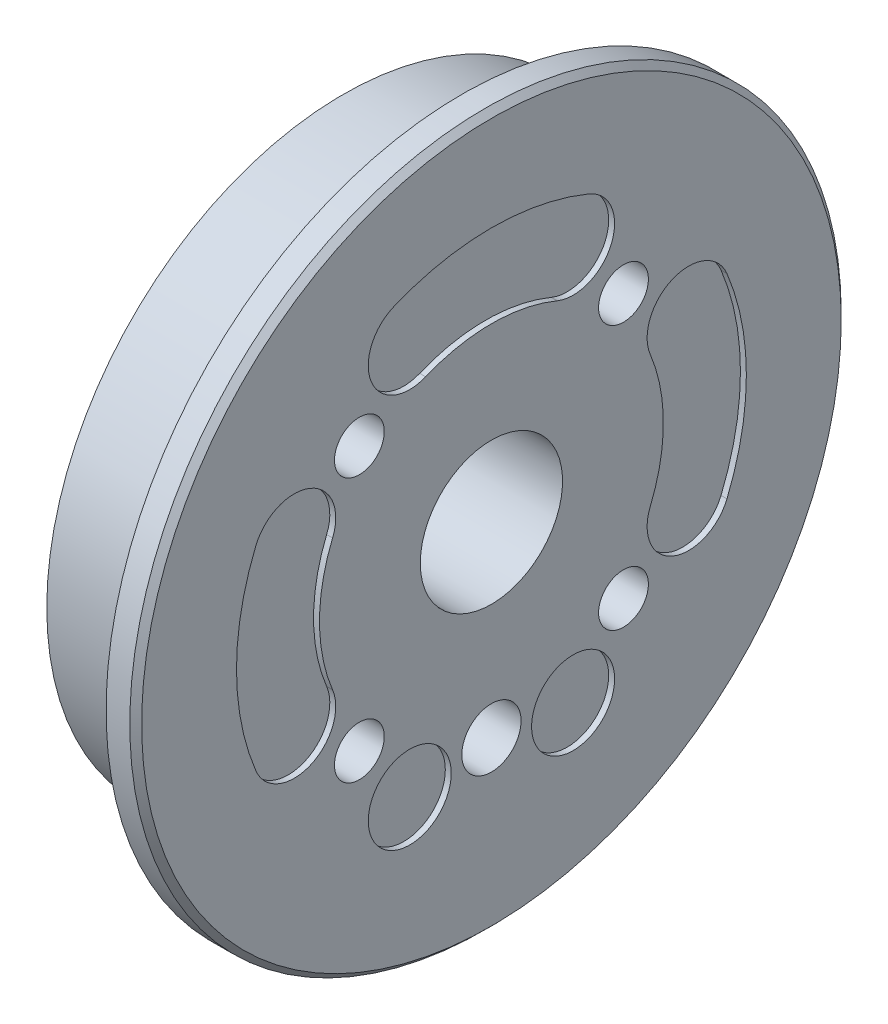
SolidWorks part; units mm, degrees
ref_plane "Front Plane" through (0, 0, 0) normal (0, 0, 1) x (1, 0, 0)
ref_plane "Top Plane" through (0, 0, 0) normal (0, 1, 0) x (1, 0, 0)
ref_plane "Right Plane" through (0, 0, 0) normal (1, 0, 0) x (0, 0, -1)
sketch "Sketch1" plane through (0, 0, 0) normal (0, 0, 1) x (1, 0, 0)
  line L0 (10, 30) -> (10, 0)
  line L1 (10, 0) -> (12.5, 0)
  line L2 (12.5, 0) -> (12.5, 30)
  line L3 (12.5, 30) -> (10, 30)
  line L4 (10, 0) -> (12.5, 0) construction
revolve "Revolve1" add sketch "Sketch1" angle 360 about L4
sketch "Sketch2" plane through (10, 0, 0) normal (-1, 0, 0) x (0, 0, 1)
  circle A0 centre (0, 0) radius 25
extrude "Boss-Extrude1" add sketch "Sketch2" along normal blind 10
sketch "Sketch3" plane through (12.5, 0, 0) normal (1, 0, 0) x (0, 0, -1)
  arc A0 (13.3963, 5.5489) -> (13.3963, -5.5489) centre (0, 0) cw
  arc A1 (13.3963, -5.5489) -> (19.8634, -8.2277) centre (16.6298, -6.8883) ccw
  arc A2 (19.8634, -8.2277) -> (19.8634, 8.2277) centre (0, 0) ccw
  arc A3 (19.8634, 8.2277) -> (13.3963, 5.5489) centre (16.6298, 6.8883) ccw
extrude "Cut-Extrude1" cut sketch "Sketch3" against normal blind 0.5
sketch "Sketch4" plane through (12.5, 0, 0) normal (1, 0, 0) x (0, 0, -1)
  arc A0 (-5.5489, 13.3963) -> (5.5489, 13.3963) centre (0, 0) cw
  arc A1 (5.5489, 13.3963) -> (8.2277, 19.8634) centre (6.8883, 16.6298) ccw
  arc A2 (8.2277, 19.8634) -> (-8.2277, 19.8634) centre (0, 0) ccw
  arc A3 (-8.2277, 19.8634) -> (-5.5489, 13.3963) centre (-6.8883, 16.6298) ccw
extrude "Cut-Extrude2" cut sketch "Sketch4" against normal blind 0.5
sketch "Sketch5" plane through (12.5, 0, 0) normal (1, 0, 0) x (0, 0, -1)
  arc A0 (-13.3963, -5.5489) -> (-13.3963, 5.5489) centre (0, 0) cw
  arc A1 (-13.3963, 5.5489) -> (-19.8634, 8.2277) centre (-16.6298, 6.8883) ccw
  arc A2 (-19.8634, 8.2277) -> (-19.8634, -8.2277) centre (0, 0) ccw
  arc A3 (-19.8634, -8.2277) -> (-13.3963, -5.5489) centre (-16.6298, -6.8883) ccw
extrude "Cut-Extrude3" cut sketch "Sketch5" against normal blind 0.5
hole_wizard "Ø12.0 (12) Diameter Hole1" positions "Sketch7" profile "Sketch6" hole size "Ø12.0" standard "ANSI Metric"
sketch "Sketch7" plane through (0, 0, 0) normal (-1, 0, 0) x (0, 0, 1)
  point P0 (0, 0)
sketch "Sketch6" plane through (0, 0, 0) normal (0, 1, 0) x (0, 0, 1)
  line L0 (0, 0) -> (0, 12.5)
  line L1 (0, 12.5) -> (6, 12.5)
  line L2 (6, 12.5) -> (6, 0)
  line L5 (6, 0) -> (0, 0)
  line L11 (0, -6.35) -> (0, 107.95) construction
  dimension "Thru Hole Dia." = 12
  dimension "Thru Hole Depth" = 12.5
hole_wizard "Ø7.0 (7) Diameter Hole1" positions "Sketch9" profile "Sketch8" hole size "Ø7.0" standard "ANSI Metric"
sketch "Sketch9" plane through (12.5, 0, 0) normal (1, 0, 0) x (0, 0, -1)
  point P0 (-6.8883, -16.6298)
  point P1 (6.8883, -16.6298)
sketch "Sketch8" plane through (12.5, -16.6298, 6.8883) normal (0, 1, 0) x (0, 0, -1)
  line L0 (0, 0) -> (0, 0.5)
  line L1 (0, 0.5) -> (3.5, 0.5)
  line L2 (3.5, 0.5) -> (3.5, 0)
  line L5 (3.5, 0) -> (0, 0)
  line L10 (0, 0.5) -> (-3.5, 0.5) construction
  line L11 (0, -6.35) -> (0, 107.95) construction
  dimension "Hole Dia." = 7
  dimension "Hole Depth" = 0.5
  dimension "Drill Angle" = 180
hole_wizard "Ø4.2 (4.2) Diameter Hole1" positions "Sketch11" profile "Sketch10" hole size "Ø4.2" standard "ANSI Metric"
sketch "Sketch11" plane through (0, 0, 0) normal (-1, 0, 0) x (0, 0, 1)
  point P0 (-11.1369, -11.1369)
  point P1 (-11.1369, 11.1369)
  point P2 (11.1369, 11.1369)
  point P3 (11.1369, -11.1369)
sketch "Sketch10" plane through (0, -11.1369, -11.1369) normal (0, 1, 0) x (0, 0, 1)
  line L0 (0, 0) -> (0, 12.5)
  line L1 (0, 12.5) -> (2.1, 12.5)
  line L2 (2.1, 12.5) -> (2.1, 0)
  line L5 (2.1, 0) -> (0, 0)
  line L11 (0, -6.35) -> (0, 107.95) construction
  dimension "Thru Hole Dia." = 4.2
  dimension "Thru Hole Depth" = 12.5
hole_wizard "Ø5.0 (5) Diameter Hole1" positions "Sketch13" profile "Sketch12" hole size "Ø5.0" standard "ANSI Metric"
sketch "Sketch13" plane through (12.5, 0, 0) normal (1, 0, 0) x (0, 0, -1)
  point P0 (0, -15.75)
sketch "Sketch12" plane through (12.5, -15.75, 0) normal (0, 1, 0) x (0, 0, -1)
  line L0 (0, 0) -> (0, 7)
  line L1 (0, 7) -> (2.5, 7)
  line L2 (2.5, 7) -> (2.5, 0)
  line L5 (2.5, 0) -> (0, 0)
  line L10 (0, 7) -> (-2.5, 7) construction
  line L11 (0, -6.35) -> (0, 107.95) construction
  dimension "Hole Dia." = 5
  dimension "Hole Depth" = 7
  dimension "Drill Angle" = 180
chamfer "Chamfer1" distance 0.5 angle 45 1 edges at (12.5, 0, -30)
